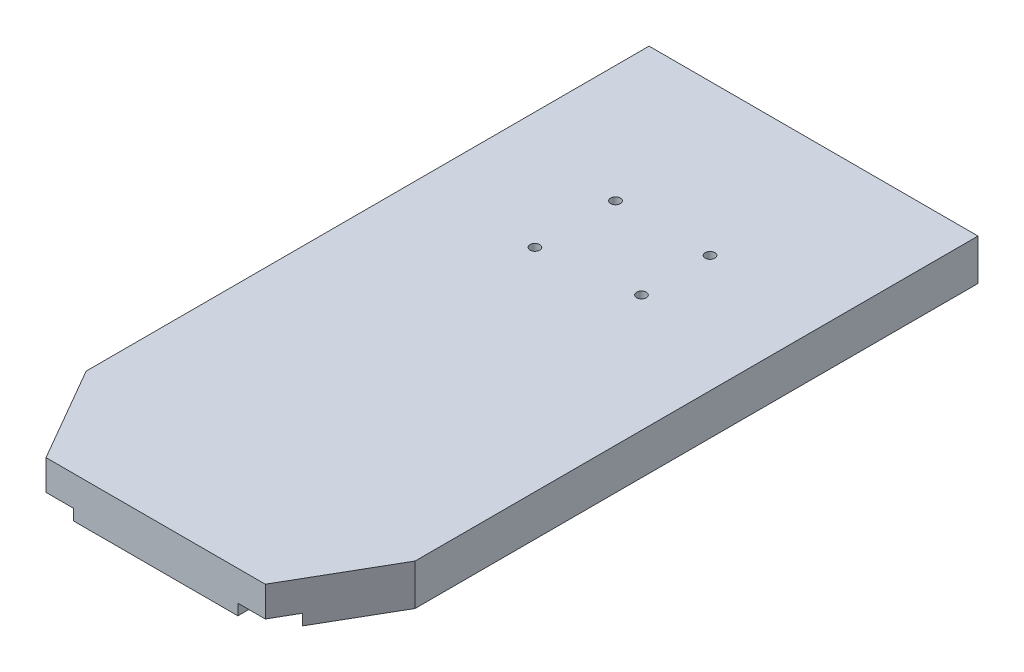
SolidWorks part; units mm, degrees
ref_plane "Front Plane" through (0, 0, 0) normal (0, 0, 1) x (1, 0, 0)
ref_plane "Top Plane" through (0, 0, 0) normal (0, 1, 0) x (1, 0, 0)
ref_plane "Right Plane" through (0, 0, 0) normal (1, 0, 0) x (0, 0, -1)
sketch "Sketch1" plane through (0, 0, 0) normal (0, 1, 0) x (1, 0, 0)
  line L1 (-76.2, -152.4) -> (76.2, -152.4)
  line L2 (-76.2, -152.4) -> (-76.2, 152.4)
  line L3 (-76.2, 152.4) -> (76.2, 152.4)
  line L4 (76.2, -152.4) -> (76.2, 152.4)
  line L5 (-76.2, -152.4) -> (76.2, 152.4) construction
  line L6 (-76.2, 152.4) -> (76.2, -152.4) construction
  point P0 (0, 0)
  dimension "D1" = 304.8
  dimension "D2" = 152.4
extrude "Boss-Extrude1" add sketch "Sketch1" along normal blind 19.05
hole_wizard "#8 Clearance Hole1" positions "Sketch2" profile "Sketch3" hole size "#8" standard "ANSI Inch" end condition through all
sketch "Sketch2" plane through (0, 19.05, 0) normal (0, 1, 0) x (1, 0, 0)
  point P0 (-21.89, 82.55)
  point P1 (21.89, 82.55)
  point P2 (-21.89, 45.212)
  point P3 (21.89, 50.8)
sketch "Sketch3" plane through (-21.89, 19.05, -82.55) normal (1, 0, 0) x (0, 0, 1)
  line L0 (0, 0) -> (0, 19.05)
  line L1 (0, 19.05) -> (2.2479, 19.05)
  line L2 (2.2479, 19.05) -> (2.2479, 0)
  line L3 (2.2479, 0) -> (0, 0)
  line L4 (0, -6.35) -> (0, 107.95) construction
  dimension "Thru Hole Dia." = 4.4958
  dimension "Thru Hole Depth" = 19.05
sketch "Sketch4" plane through (0, 0, 0) normal (0, -1, 0) x (1, 0, 0)
  line L0 (0, 0) -> (0, 152.4) construction
  line L1 (-76.2, 152.4) -> (76.2, 152.4) construction
  line L2 (-50.8, 152.4) -> (-76.2, 108.4059)
  line L3 (-76.2, -152.4) -> (-76.2, 152.4) construction
  line L4 (50.8, 152.4) -> (76.2, 108.4059)
  line L9 (76.2, -152.4) -> (76.2, 152.4)
  line L10 (76.2, 152.4) -> (-76.2, 152.4)
  line L11 (-76.2, 152.4) -> (-76.2, -152.4)
  line L12 (-76.2, -152.4) -> (76.2, -152.4)
  line L13 (76.2, -152.4) -> (76.2, 152.4)
  line L14 (76.2, 152.4) -> (-76.2, 152.4)
  line L15 (-76.2, 152.4) -> (-76.2, -152.4)
  line L16 (-76.2, -152.4) -> (76.2, -152.4)
  line M10 (76.2, -152.4) -> (76.2, 152.4)
  line M11 (76.2, 152.4) -> (-76.2, 152.4)
  line M12 (-76.2, 152.4) -> (-76.2, -152.4)
  dimension "D1" = 50.8
  dimension "D2" = 30
  dimension "D3" = 0
extrude "Cut-Extrude1" cut sketch "Sketch4" against normal through all contours L4 M11 M10 | L2 M11 M12
sketch "Sketch5" plane through (0, 0, 0) normal (0, -1, 0) x (1, 0, 0)
  line L0 (0, -152.4) -> (0, 152.4) construction
  line L1 (76.2, -152.4) -> (-76.2, -152.4) construction
  line L2 (-50.8, 152.4) -> (50.8, 152.4) construction
  line L3 (57.15, 152.4) -> (57.15, -152.4)
  line L4 (-57.15, 152.4) -> (-38.1, 152.4)
  line L5 (-57.15, 152.4) -> (-57.15, -152.4)
  line L6 (-57.15, -152.4) -> (-38.1, -152.4)
  line L7 (-38.1, 152.4) -> (-38.1, -152.4)
  line L8 (57.15, 152.4) -> (38.1, 152.4)
  line L9 (38.1, 152.4) -> (38.1, -152.4)
  line L10 (57.15, -152.4) -> (38.1, -152.4)
  dimension "D1" = 19.05
  dimension "D2" = 38.1
extrude "Cut-Extrude2" cut sketch "Sketch5" against normal blind 5.08 contours L3 L8 L9 L10 | L5 L4 L7 L6
